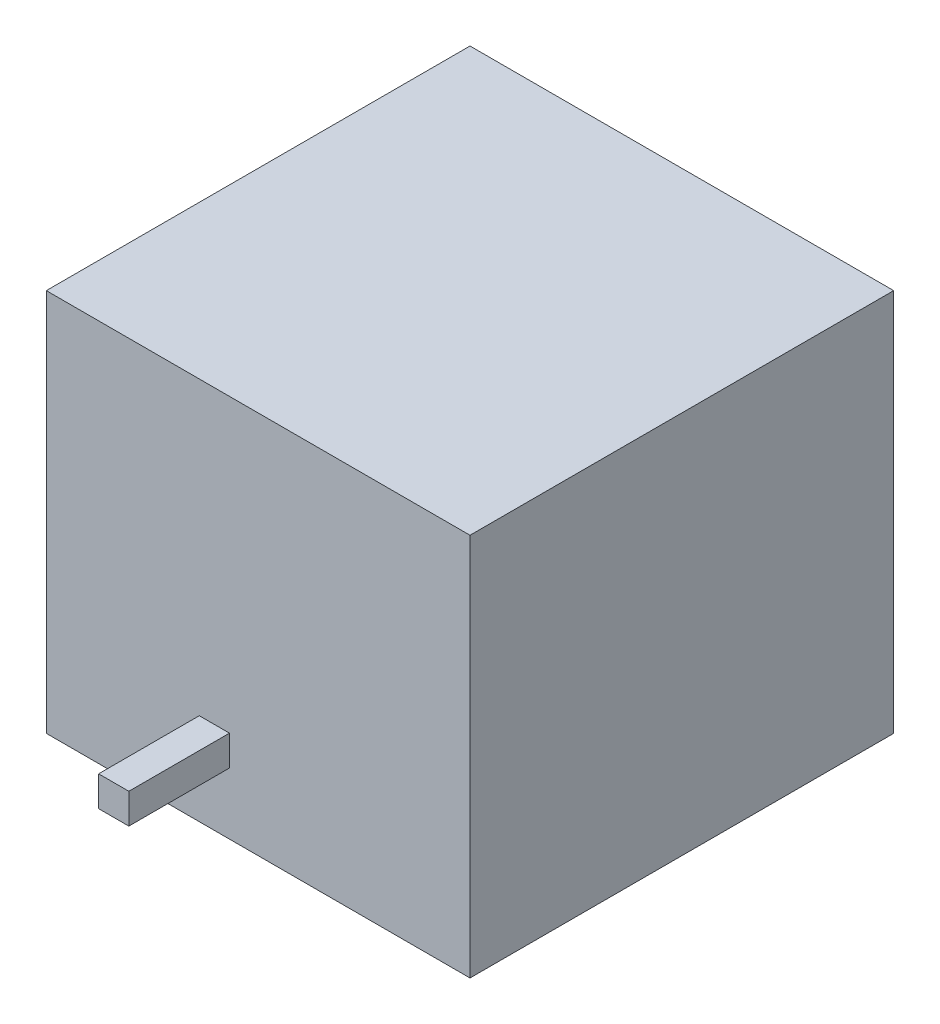
SolidWorks part; units mm, degrees
ref_plane "Front Plane" through (0, 0, 0) normal (0, 0, 1) x (1, 0, 0)
ref_plane "Top Plane" through (0, 0, 0) normal (0, 1, 0) x (1, 0, 0)
ref_plane "Right Plane" through (0, 0, 0) normal (1, 0, 0) x (0, 0, -1)
sketch "Sketch2" plane through (0, 0, 0) normal (0, 1, 0) x (1, 0, 0)
  line L1 (0, 0) -> (42.1, 0)
  line L2 (0, 0) -> (0, 42.1)
  line L3 (0, 42.1) -> (42.1, 42.1)
  line L4 (42.1, 0) -> (42.1, 42.1)
  dimension "D1" = 42.1
  dimension "D2" = 42.1
extrude "Boss-Extrude1" add sketch "Sketch2" along normal blind 38.1
sketch "Sketch4" plane through (0, 0, 0) normal (0, 0, 1) x (1, 0, 0)
  line L0 (42.1, 38.1) -> (42.1, 0) construction
  line L1 (0, 38.1) -> (42.1, 38.1) construction
  line L3 (15.2, 9.12) -> (18.2, 9.12)
  line L4 (15.2, 9.12) -> (15.2, 6.12)
  line L5 (15.2, 6.12) -> (18.2, 6.12)
  line L6 (18.2, 9.12) -> (18.2, 6.12)
  line L7 (15.2, 9.12) -> (18.2, 6.12) construction
  line L8 (15.2, 6.12) -> (18.2, 9.12) construction
  circle A0 centre (16.7, 7.62) radius 1.5 construction
  point P10 (16.7, 7.62)
  dimension "D1" = 3
  dimension "D2" = 25.4
  dimension "D3" = 30.48
  dimension "D4" = 3
  dimension "D5" = 3
extrude "Boss-Extrude2" add sketch "Sketch4" along normal blind 10
